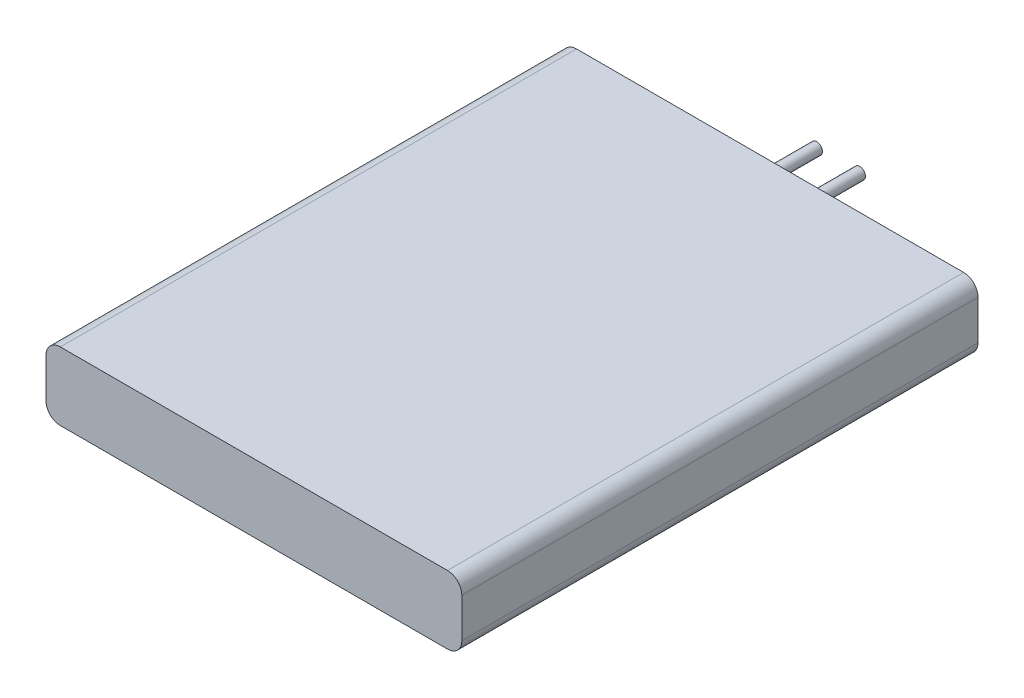
SolidWorks part; units mm, degrees
ref_plane "Front Plane" through (0, 0, 0) normal (0, 0, 1) x (1, 0, 0)
ref_plane "Top Plane" through (0, 0, 0) normal (0, 1, 0) x (1, 0, 0)
ref_plane "Right Plane" through (0, 0, 0) normal (1, 0, 0) x (0, 0, -1)
sketch "Sketch1" plane through (0, 0, 0) normal (0, 1, 0) x (1, 0, 0)
  line L1 (-14.5, -18) -> (14.5, -18)
  line L2 (-14.5, -18) -> (-14.5, 18)
  line L3 (-14.5, 18) -> (14.5, 18)
  line L4 (14.5, -18) -> (14.5, 18)
  line L5 (-14.5, -18) -> (14.5, 18) construction
  line L6 (-14.5, 18) -> (14.5, -18) construction
  point P0 (0, 0)
  dimension "D1" = 36
  dimension "D2" = 29
extrude "Boss-Extrude1" add sketch "Sketch1" along normal blind 4.75
sketch "Sketch2" plane through (0, 0, -18) normal (0, 0, -1) x (-1, 0, 0)
  line L0 (0, 0) -> (0, 4.75) construction
  line L1 (-14.5, 4.75) -> (14.5, 4.75) construction
  line L2 (-14.5, 2.375) -> (14.5, 2.375) construction
  line L3 (-14.5, 4.75) -> (-14.5, 0) construction
  line L4 (14.5, 4.75) -> (14.5, 0) construction
  circle A0 centre (1.5, 2.375) radius 0.4
  circle A1 centre (-1.5, 2.375) radius 0.4
  dimension "D2" = 0.8
  dimension "D1" = 1.5
extrude "Boss-Extrude2" add sketch "Sketch2" along normal blind 4.75
fillet "Fillet1" radius 1 4 edges at (-14.5, 0, 0) (-14.5, 4.75, 0) (14.5, 0, 0) (14.5, 4.75, 0)
